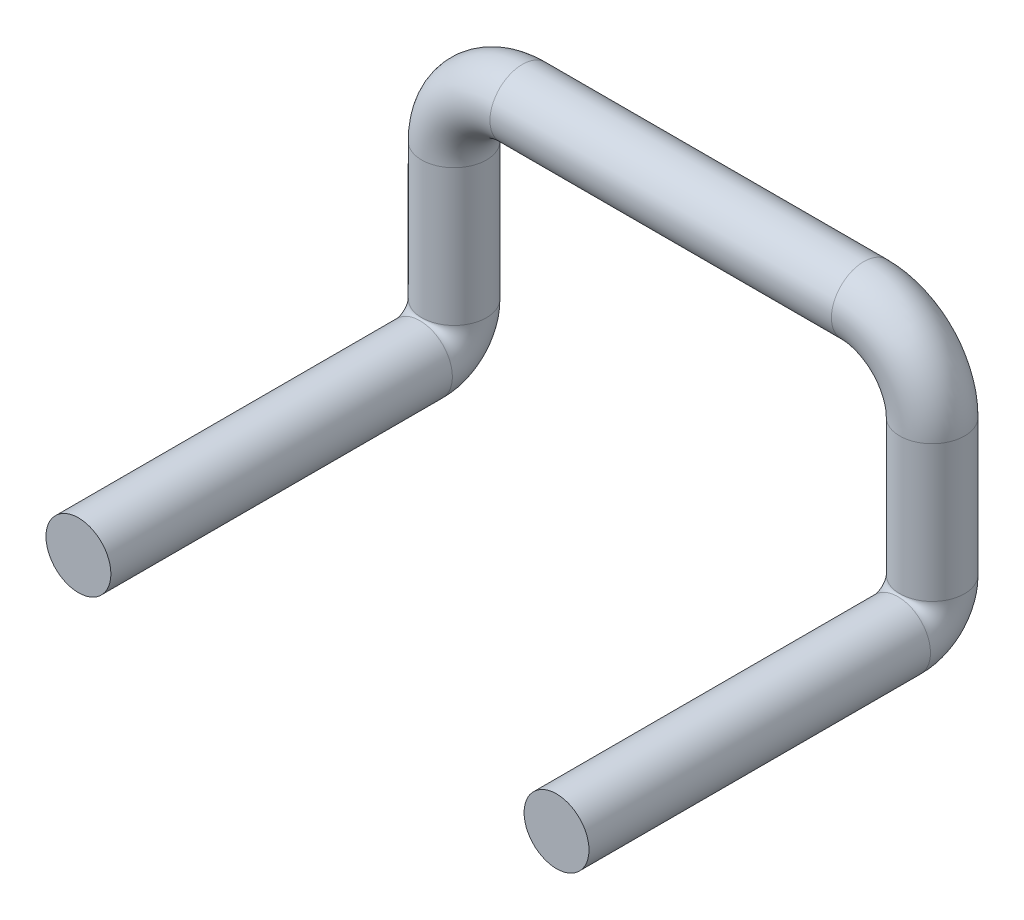
SolidWorks part; units mm, degrees
material "Copper"
ref_plane "Front Plane" through (0, 0, 0) normal (0, 0, 1) x (1, 0, 0)
ref_plane "Top Plane" through (0, 0, 0) normal (0, 1, 0) x (1, 0, 0)
ref_plane "Right Plane" through (0, 0, 0) normal (1, 0, 0) x (0, 0, -1)
sketch "Sketch1" plane through (0, 0, 0) normal (0, 0, 1) x (1, 0, 0)
  line L0 (0, 0) -> (0, 4)
  line L1 (2, 6) -> (12, 6)
  line L2 (14, 4) -> (14, 0)
  arc A0 (12, 6) -> (14, 4) centre (12, 4) cw
  arc A1 (0, 4) -> (2, 6) centre (2, 4) cw
  point P3 (14, 0)
  point P8 (14, 6)
  point P11 (0, 6)
  dimension "D3" = 2
  dimension "D1" = 6
  dimension "D2" = 14
sketch "Sketch2" plane through (0, 0, 0) normal (1, 0, 0) x (0, 0, -1)
  line L0 (-1, -1) -> (-11, -1)
  line L1 (0, 0) -> (0, 4) construction
  arc A0 (0, 0) -> (-1, -1) centre (-1, 0) cw
  dimension "D1" = 1
  dimension "D2" = 10
ref_plane "Plane1" through (0, 0, 0) normal (0, 0, 1) x (1, 0, 0)
ref_plane "Plane2" through (14, 0, 0) normal (-1, 0, 0) x (0, -1, 0)
sketch "Sketch3" plane through (14, 0, 0) normal (-1, 0, 0) x (0, -1, 0)
  line L0 (1, 1) -> (1, 11) construction
  line L1 (1, 1) -> (1, 11)
  arc A0 (0, 0) -> (1, 1) centre (0, 1) ccw construction
  arc A1 (0, 0) -> (1, 1) centre (0, 1) ccw
ref_plane "Plane3" through (0, 0, 11) normal (0, 0, 1) x (1, 0, 0)
sketch "Sketch4" plane through (0, 0, 11) normal (0, 0, 1) x (1, 0, 0)
  line L0 (14, 0) -> (14, -1) construction
  line L1 (2, 6) -> (12, 6) construction
  circle A0 centre (14, -1) radius 1.13
  dimension "D1" = 2.26
  dimension "D2" = 7
sweep "Sweep5" add path "Sketch1" circular profile diameter 1.9 parameters "D3"=1.9
sweep "Sweep6" add path "Sketch3" circular profile diameter 1.9 parameters "D3"=1.9
sweep "Sweep7" add path "Sketch2" circular profile diameter 1.9 parameters "D3"=1.9
